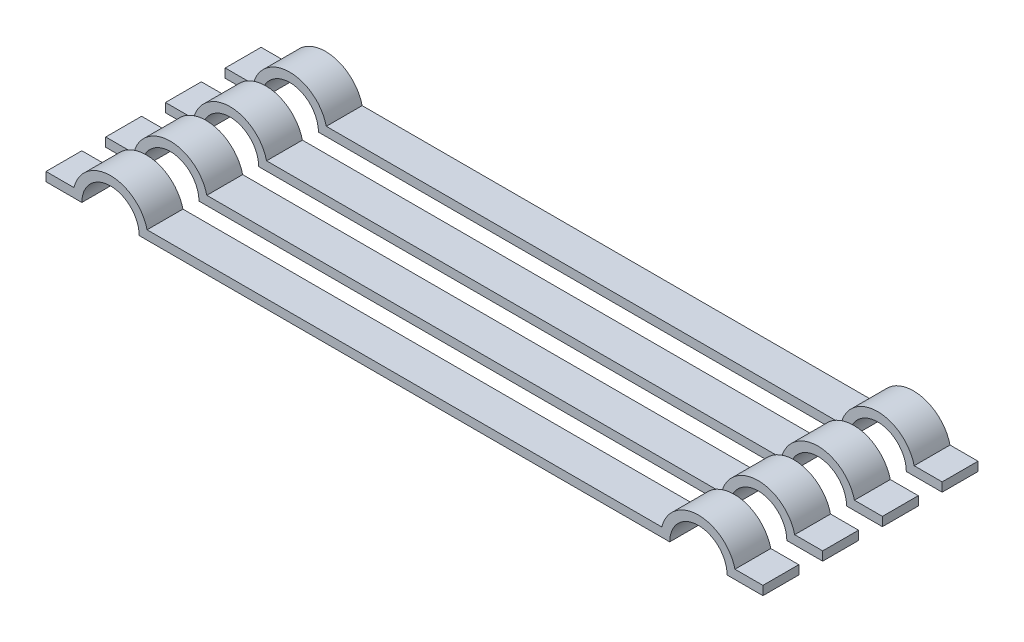
SolidWorks part; units mm, degrees
material "Chrome Stainless Steel"
ref_plane "Front Plane" through (0, 0, 0) normal (0, 0, 1) x (1, 0, 0)
ref_plane "Top Plane" through (0, 0, 0) normal (0, 1, 0) x (1, 0, 0)
ref_plane "Right Plane" through (0, 0, 0) normal (1, 0, 0) x (0, 0, -1)
sketch "Sketch1" plane through (0, 0, 0) normal (0, 0, 1) x (1, 0, 0)
  line L0 (55, 0) -> (-55, 0) construction
  line L1 (0, -55) -> (0, 55) construction
  line L2 (-7.4, 0) -> (7.4, 0)
  line L3 (9, 0) -> (10, 0)
  line L4 (-9, 0) -> (-10, 0)
  arc A0 (-7.4, 0) -> (-9, 0) centre (-8.2, 0) ccw
  arc A1 (9, 0) -> (7.4, 0) centre (8.2, 0) ccw
  dimension "D1" = 1.6
  dimension "D2" = 8.2
  dimension "D3" = 8.2
  dimension "D4" = 1
extrude "Extrude-Thin1" add sketch "Sketch1" along normal blind 6 thin thin type one direction wall 0.25
sketch "Sketch2" plane through (0, 0, 0) normal (0, 1, 0) x (1, 0, 0)
  line L0 (-0.5775, 0) -> (0.5775, 0) construction
  line L1 (-10, -1) -> (10, -1)
  line L2 (-10, -1) -> (-10, -1.6667)
  line L3 (-10, -1.6667) -> (10, -1.6667)
  line L4 (10, -1) -> (10, -1.6667)
  line L5 (-10, -2.6667) -> (10, -2.6667)
  line L6 (-10, -2.6667) -> (-10, -3.3333)
  line L7 (-10, -3.3333) -> (10, -3.3333)
  line L8 (10, -2.6667) -> (10, -3.3333)
  line L9 (-10, -4.3333) -> (10, -4.3333)
  line L10 (-10, -4.3333) -> (-10, -5)
  line L11 (-10, -5) -> (10, -5)
  line L12 (10, -4.3333) -> (10, -5)
  line L13 (0, -0.5775) -> (0, 0.5775) construction
  dimension "D1" = 1
  dimension "D2" = 1
  dimension "D3" = 1
  dimension "D4" = 0.6667
  dimension "D5" = 10
  dimension "D6" = 10
extrude "Extrude1" cut sketch "Sketch2" along normal through all
